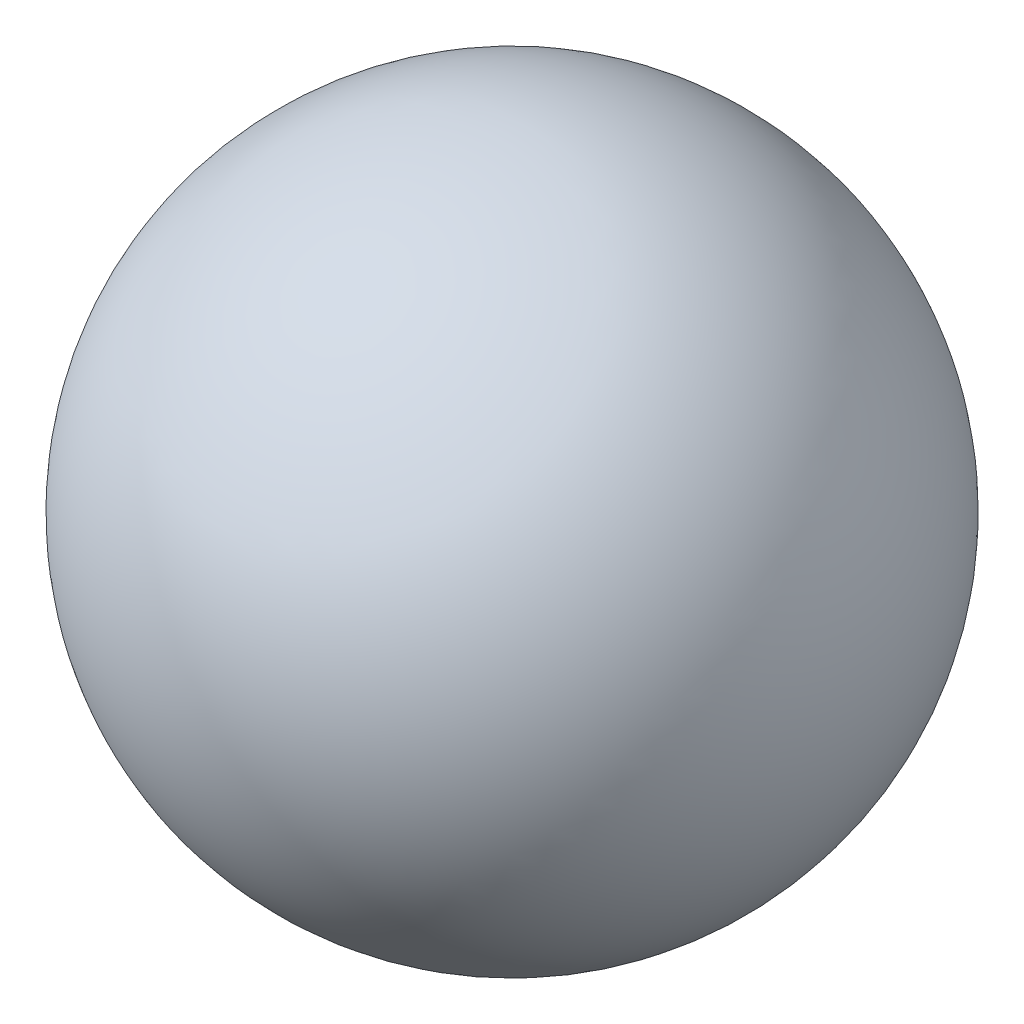
SolidWorks part; units mm, degrees
ref_plane "Front Plane" through (0, 0, 0) normal (0, 0, 1) x (1, 0, 0)
ref_plane "Top Plane" through (0, 0, 0) normal (0, 1, 0) x (1, 0, 0)
ref_plane "Right Plane" through (0, 0, 0) normal (1, 0, 0) x (0, 0, -1)
sketch "Sketch1" plane through (0, 0, 0) normal (0, 1, 0) x (1, 0, 0)
  line L0 (0, 0) -> (0, 15)
  arc A0 (0, 15) -> (0, 0) centre (0, 7.5) cw
  dimension "D1" = 15
revolve "Revolve1" add sketch "Sketch1" angle 360 about L0
